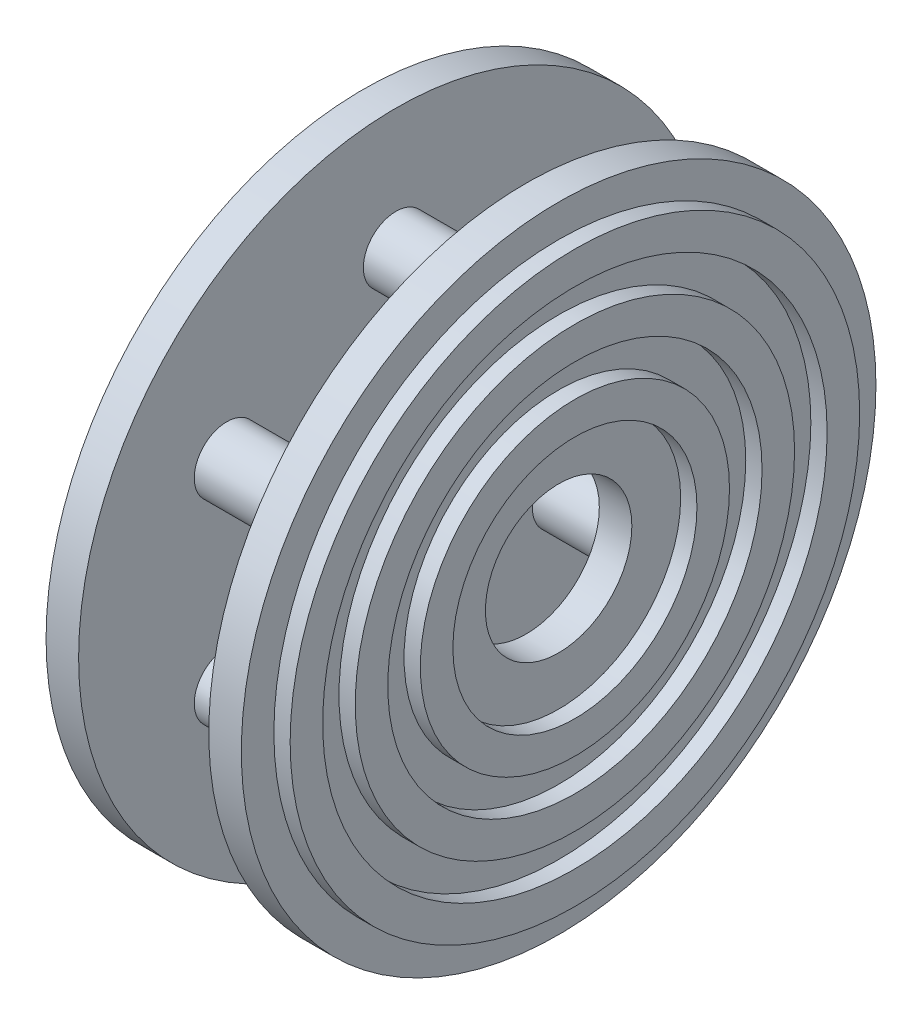
SolidWorks part; units mm, degrees
ref_plane "Front Plane" through (0, 0, 0) normal (0, 0, 1) x (1, 0, 0)
ref_plane "Top Plane" through (0, 0, 0) normal (0, 1, 0) x (1, 0, 0)
ref_plane "Right Plane" through (0, 0, 0) normal (1, 0, 0) x (0, 0, -1)
sketch "Sketch1" plane through (0, 0, 0) normal (1, 0, 0) x (0, 0, -1)
  circle A0 centre (0, 0) radius 2.25
  circle A1 centre (0, 0) radius 9.75
  circle A4 centre (0, 0) radius 2.25 construction
  circle A5 centre (0, 0) radius 9.75 construction
extrude "Boss-Extrude1" add sketch "Sketch1" along normal blind 1
sketch "Sketch2" plane through (1, 0, 0) normal (1, 0, 0) x (0, 0, -1)
  arc A31 (-8.6969, -0.9629) -> (8.6969, 0.9629) centre (0, 0) ccw
  arc A32 (-7.7029, -0.8529) -> (7.7029, 0.8529) centre (0, 0) ccw
  arc A33 (-6.709, -0.7428) -> (6.709, 0.7428) centre (0, 0) ccw
  arc A34 (-5.7151, -0.6328) -> (5.7151, 0.6328) centre (0, 0) ccw
  arc A35 (-4.7211, -0.5227) -> (4.7211, 0.5227) centre (0, 0) ccw
  arc A36 (-3.7272, -0.4127) -> (3.7272, 0.4127) centre (0, 0) ccw
  circle A37 centre (0, 0) radius 8.75
  circle A38 centre (0, 0) radius 7.75
  circle A39 centre (0, 0) radius 6.75
  circle A40 centre (0, 0) radius 5.75
  circle A41 centre (0, 0) radius 4.75
  circle A42 centre (0, 0) radius 3.75
extrude "Boss-Extrude2" add sketch "Sketch2" along normal blind 0.5 contours A31 A37 A38 A32 | A33 A39 A40 A34 | A35 A41 A42 A36
sketch "Sketch3" plane through (0, 0, 0) normal (-1, 0, 0) x (0, 0, 1)
  line L0 (0, 2.25) -> (0, 9.75) construction
  circle A4 centre (0, 0) radius 2.25 construction
  circle A5 centre (0, 0) radius 9.75 construction
  circle A6 centre (0, 6) radius 1
  circle A7 centre (5.1962, 3) radius 1
  circle A8 centre (5.1962, -3) radius 1
  circle A9 centre (0, -6) radius 1
  circle A10 centre (-5.1962, -3) radius 1
  circle A11 centre (-5.1962, 3) radius 1
  dimension "D1" = 2
  dimension "D2" = 6
extrude "Boss-Extrude3" add sketch "Sketch3" along normal blind 4 contours A6 L0 | L0 A6 | A11 | A10 | A9 | A8 | A7
sketch "Sketch4" plane through (-4, 0, 0) normal (-1, 0, 0) x (0, 0, 1)
  circle A0 centre (0, 0) radius 9.75 construction
  circle A1 centre (0, 0) radius 2.25 construction
  circle A2 centre (0, 0) radius 9.75
  circle A3 centre (0, 0) radius 2.25
extrude "Boss-Extrude4" add sketch "Sketch4" along normal blind 1
